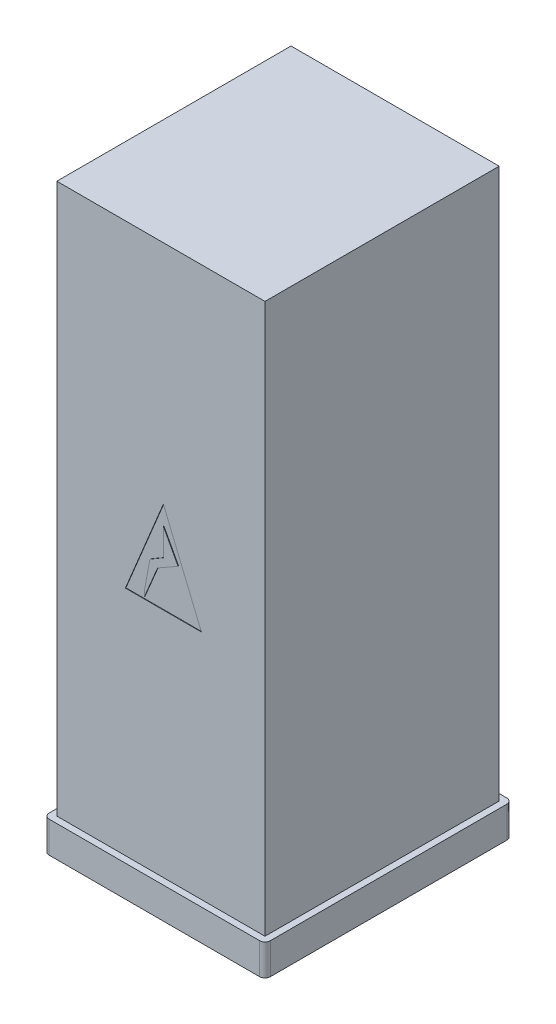
SolidWorks part; units mm, degrees
ref_plane "Alzado" through (0, 0, 0) normal (0, 0, 1) x (1, 0, 0)
ref_plane "Planta" through (0, 0, 0) normal (0, 1, 0) x (1, 0, 0)
ref_plane "Vista lateral" through (0, 0, 0) normal (1, 0, 0) x (0, 0, -1)
sketch "Croquis1" plane through (0, 0, 0) normal (0, 1, 0) x (1, 0, 0)
  line L1 (-400, 450) -> (400, 450)
  line L2 (-400, 450) -> (-400, -450)
  line L3 (-400, -450) -> (400, -450)
  line L4 (400, 450) -> (400, -450)
  line L5 (-400, 450) -> (400, -450) construction
  line L6 (-400, -450) -> (400, 450) construction
  point P0 (0, 0)
  dimension "D1" = 900
  dimension "D2" = 800
extrude "Saliente-Extruir1" add sketch "Croquis1" along normal blind 2113
shell "Vaciado2" thickness 10
sketch "Croquis2" plane through (0, 0, 450) normal (0, 0, 1) x (1, 0, 0)
  line L0 (-390, 2103) -> (390, 2103)
  line L1 (390, 2103) -> (390, 10)
  line L2 (390, 10) -> (-390, 10)
  line L3 (-390, 10) -> (-390, 2103)
extrude "Saliente-Extruir2" add sketch "Croquis2" against normal blind 5
sketch "Croquis3" plane through (0, 0, 450) normal (0, 0, 1) x (1, 0, 0)
  line L0 (-136.51, 890.5201) -> (155.4697, 890.5201)
  line L1 (155.4697, 890.5201) -> (9.4799, 1243.171)
  line L2 (9.4799, 1243.171) -> (-136.51, 890.5201)
  line L3 (-63.1768, 920.1946) -> (-42.1695, 1034.0418)
  line L4 (-42.1695, 1034.0418) -> (9.4799, 1064.1699)
  line L5 (9.4799, 1064.1699) -> (9.4799, 1169.412)
  line L6 (9.4799, 1169.412) -> (65.9663, 1064.1699)
  line L7 (65.9663, 1064.1699) -> (-12.5323, 1019.6237)
  line L8 (-12.5323, 1019.6237) -> (-63.1768, 898.9131)
  line L9 (-63.1768, 898.9131) -> (-63.1768, 920.1946)
extrude "Cortar-Extruir1" cut sketch "Croquis3" against normal blind 2
sketch "Croquis4" plane through (0, 0, 0) normal (0, -1, 0) x (1, 0, 0)
  line L0 (-400, -450) -> (-400, 450) construction
  line L1 (-404.3565, 475) -> (404.3565, 475)
  line L2 (-425, 454.3565) -> (-425, -454.3565)
  line L3 (-404.3565, -475) -> (404.3565, -475)
  line L4 (425, 454.3565) -> (425, -454.3565)
  line L5 (-425, 475) -> (425, -475) construction
  line L6 (-425, -475) -> (425, 475) construction
  line L7 (-400, 450) -> (400, 450) construction
  arc A0 (404.3565, 475) -> (425, 454.3565) centre (404.3565, 454.3565) cw
  arc A1 (404.3565, -475) -> (425, -454.3565) centre (404.3565, -454.3565) ccw
  arc A2 (-425, -454.3565) -> (-404.3565, -475) centre (-404.3565, -454.3565) ccw
  arc A3 (-404.3565, 475) -> (-425, 454.3565) centre (-404.3565, 454.3565) ccw
  point P0 (0, 0)
  dimension "D3" = 20.6435
  dimension "D1" = 25
  dimension "D2" = 25
extrude "Saliente-Extruir3" add sketch "Croquis4" along normal blind 120
